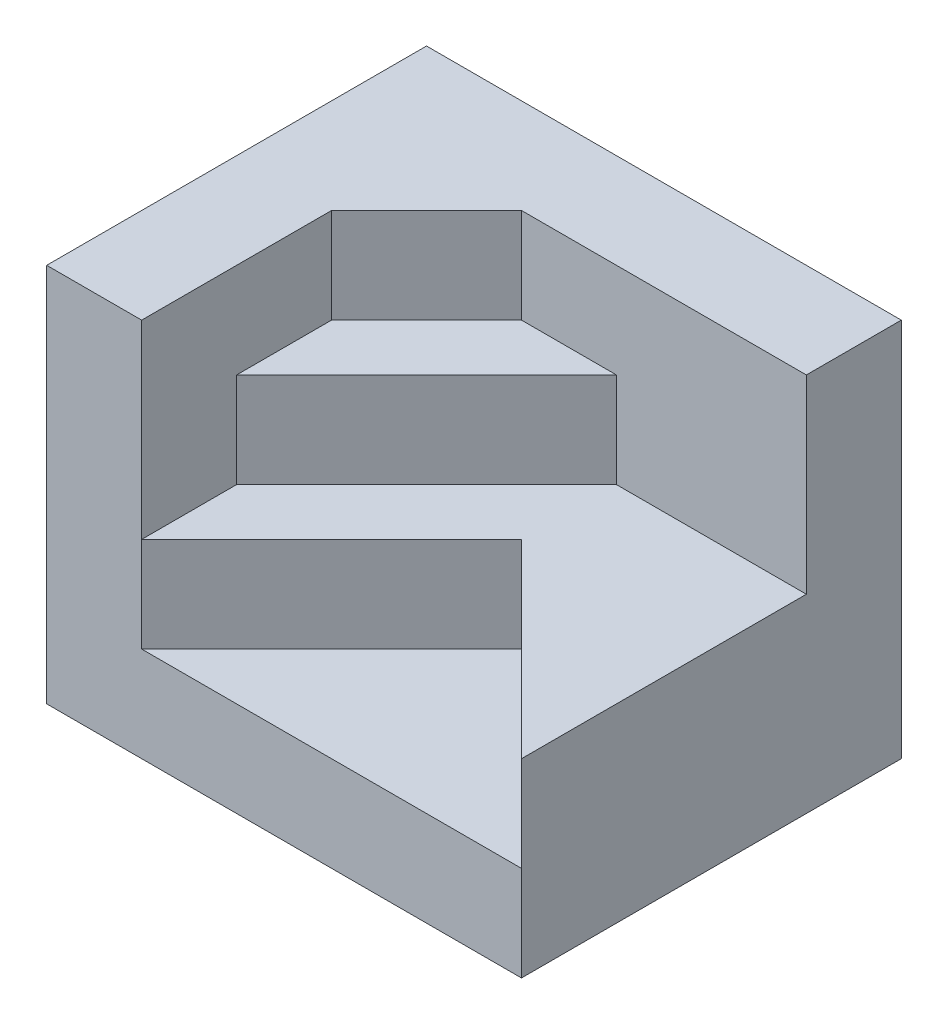
SolidWorks part; units mm, degrees
ref_plane "前基準面" through (0, 0, 0) normal (0, 0, 1) x (1, 0, 0)
ref_plane "上基準面" through (0, 0, 0) normal (0, 1, 0) x (1, 0, 0)
ref_plane "右基準面" through (0, 0, 0) normal (1, 0, 0) x (0, 0, -1)
sketch "草圖1" plane through (0, 0, 0) normal (0, 1, 0) x (1, 0, 0)
  line L1 (-25, -20) -> (25, -20)
  line L2 (-25, -20) -> (-25, 20)
  line L3 (-25, 20) -> (25, 20)
  line L4 (25, -20) -> (25, 20)
  line L5 (-25, -20) -> (25, 20) construction
  line L6 (-25, 20) -> (25, -20) construction
  point P0 (0, 0)
  dimension "D1" = 50
  dimension "D2" = 40
extrude "填料-伸長1" add sketch "草圖1" along normal blind 40
sketch "草圖2" plane through (0, 40, 0) normal (0, 1, 0) x (1, 0, 0)
  line L0 (25, -20) -> (5, 0)
  line L1 (5, 0) -> (-15, -20)
  line L2 (-25, -20) -> (25, -20) construction
  line L3 (-15, -20) -> (25, -20)
  line L4 (-25, 20) -> (-25, -20) construction
  point P9 (5, -20)
  dimension "D1" = 20
  dimension "D2" = 10
extrude "除料-伸長1" cut sketch "草圖2" against normal blind 30
sketch "草圖3" plane through (0, 40, 0) normal (0, 1, 0) x (1, 0, 0)
  line L0 (25, 10) -> (-5, 10)
  line L1 (25, -20) -> (25, 20) construction
  line L2 (-5, 10) -> (-15, 0)
  line L3 (-15, 0) -> (-15, -20)
  line L4 (25, 20) -> (-25, 20) construction
  dimension "D1" = 10
  dimension "D2" = 10
  dimension "D3" = 10
extrude "除料-伸長2" cut sketch "草圖3" against normal blind 20 and the other way through all
sketch "草圖4" plane through (0, 20, 0) normal (0, 1, 0) x (1, 0, 0)
  line L0 (-15, -10) -> (5, 10)
  line L1 (-15, -20) -> (-15, 0) construction
  line L2 (-5, 10) -> (25, 10) construction
  line L4 (-15, -10) -> (-15, 0)
  line L5 (-15, 0) -> (-5, 10)
  line L6 (-5, 10) -> (5, 10)
  line L7 (5, 10) -> (5.1305, 10.0128)
  dimension "D1" = 10
extrude "填料-伸長2" add sketch "草圖4" along normal blind 10 contours L6 L5 L4 L0
